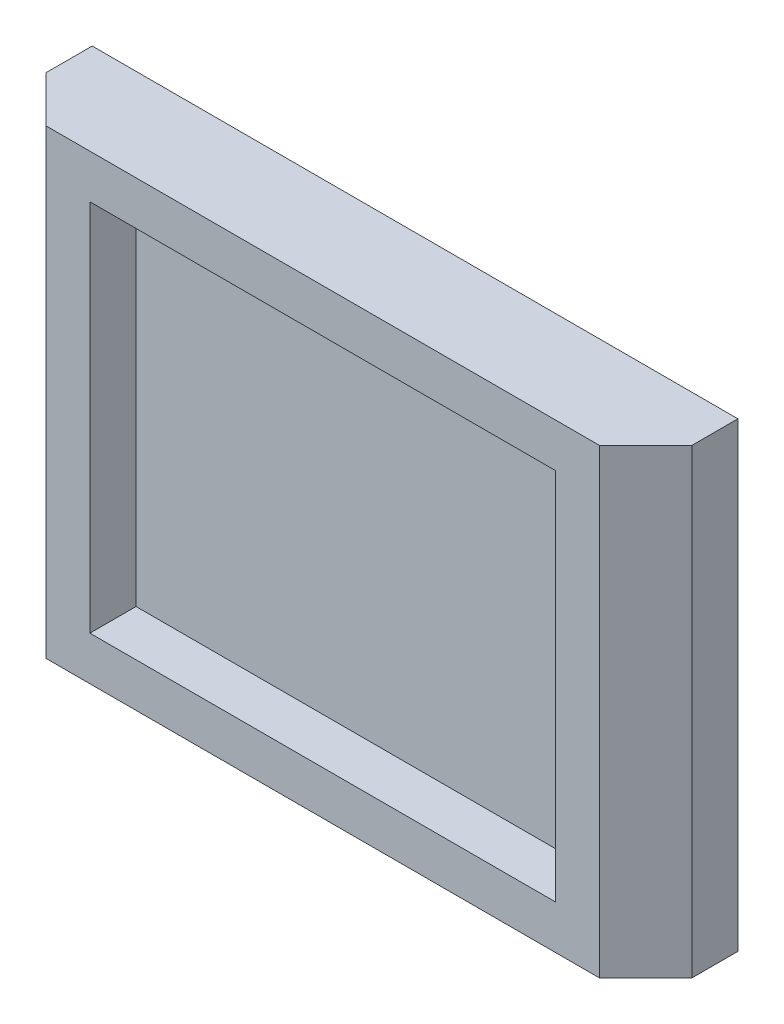
SolidWorks part; units mm, degrees
ref_plane "Ebene vorne" through (0, 0, 0) normal (0, 0, 1) x (1, 0, 0)
ref_plane "Ebene oben" through (0, 0, 0) normal (0, 1, 0) x (1, 0, 0)
ref_plane "Ebene rechts" through (0, 0, 0) normal (1, 0, 0) x (0, 0, -1)
sketch "Skizze1" plane through (0, 0, 0) normal (0, 0, 1) x (1, 0, 0)
  line L0 (-77.2711, 0) -> (59.079, 0) construction
  line L1 (0, 36.1276) -> (0, -45.7715) construction
  line L3 (-35, 25) -> (35, 25)
  line L4 (-35, 25) -> (-35, -25)
  line L5 (-35, -25) -> (35, -25)
  line L6 (35, 25) -> (35, -25)
  dimension "D1" = 50
  dimension "D2" = 70
extrude "Aufsatz-Linear austragen1" add sketch "Skizze1" along normal blind 10
sketch "Skizze2" plane through (0, 0, 10) normal (0, 0, 1) x (1, 0, 0)
  line L0 (0, 21.7456) -> (0, -20.0225) construction
  line L1 (-25.25, 20.25) -> (25.25, 20.25)
  line L2 (-25.25, 20.25) -> (-25.25, -20.25)
  line L3 (-25.25, -20.25) -> (25.25, -20.25)
  line L4 (25.25, 20.25) -> (25.25, -20.25)
  line L5 (-19.7123, 0) -> (13.4402, 0) construction
  dimension "D1" = 50.5
  dimension "D2" = 40.5
extrude "Schnitt-Linear austragen1" cut sketch "Skizze2" against normal blind 5
chamfer "Fase2" distance 5 angle 45 2 edges at (-35, 0, 10) (35, 0, 10)
